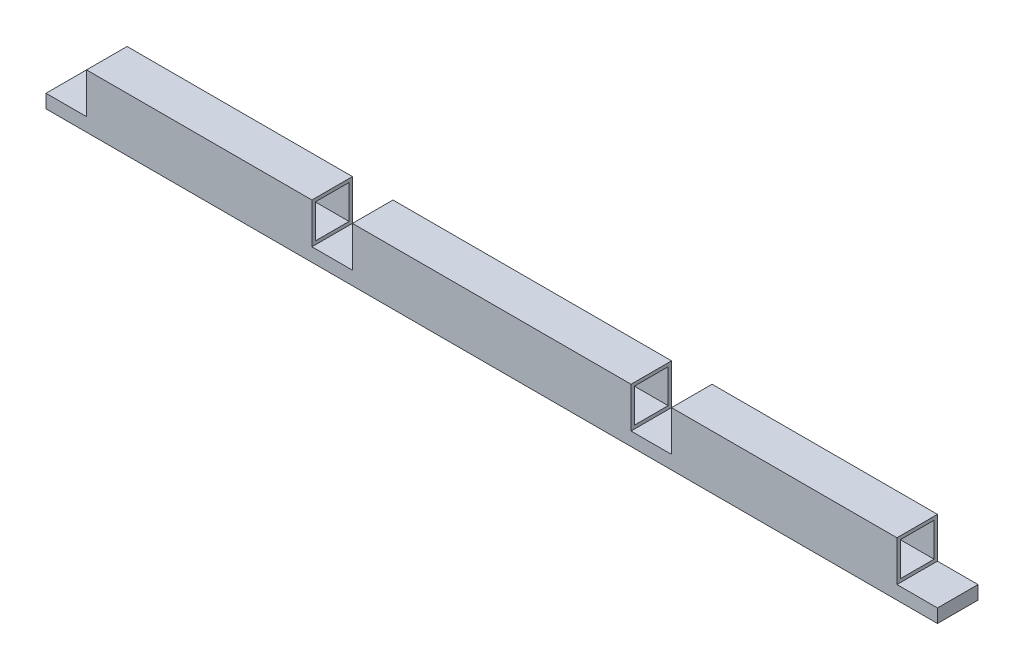
SolidWorks part; units mm, degrees
material "AISI 1020"
ref_plane "Front Plane" through (0, 0, 0) normal (0, 0, 1) x (1, 0, 0)
ref_plane "Top Plane" through (0, 0, 0) normal (0, 1, 0) x (1, 0, 0)
ref_plane "Right Plane" through (0, 0, 0) normal (1, 0, 0) x (0, 0, -1)
sketch "Sketch1" plane through (0, 0, 0) normal (0, 0, 1) x (1, 0, 0)
  line L1 (0, 0) -> (838.1, 0)
  line L2 (0, 0) -> (0, 12.7)
  line L3 (0, 12.7) -> (838.1, 12.7)
  line L4 (838.1, 0) -> (838.1, 12.7)
  dimension "D1" = 12.7
  dimension "D2" = 838.1
extrude "Boss-Extrude1" add sketch "Sketch1" against normal blind 38.1
sketch "Sketch2" plane through (0, 12.7, 0) normal (0, 1, 0) x (1, 0, 0)
  line L0 (838.1, 38.1) -> (0, 38.1) construction
  line L1 (0, 0) -> (38.1, 0) construction
  line L2 (0, 0) -> (0, 38.1) construction
  line L3 (0, 38.1) -> (38.1, 38.1) construction
  line L4 (38.1, 0) -> (38.1, 38.1) construction
  line L5 (838.1, 0) -> (0, 0) construction
  line L6 (250, 0) -> (288.1, 0) construction
  line L7 (250, 0) -> (250, 38.1) construction
  line L8 (250, 38.1) -> (288.1, 38.1) construction
  line L9 (288.1, 0) -> (288.1, 38.1) construction
  line L11 (550, 0) -> (588.1, 0) construction
  line L12 (550, 0) -> (550, 38.1) construction
  line L13 (550, 38.1) -> (588.1, 38.1) construction
  line L14 (588.1, 0) -> (588.1, 38.1) construction
  line L15 (838.1, 38.1) -> (800, 38.1) construction
  line L16 (838.1, 38.1) -> (838.1, 0) construction
  line L17 (838.1, 0) -> (800, 0) construction
  line L18 (800, 38.1) -> (800, 0) construction
  line L19 (38.1, 0) -> (250, 0)
  line L20 (38.1, 0) -> (38.1, 38.1)
  line L21 (38.1, 38.1) -> (250, 38.1)
  line L22 (250, 0) -> (250, 38.1)
  line L23 (288.1, 38.1) -> (550, 38.1)
  line L24 (288.1, 38.1) -> (288.1, 0)
  line L25 (288.1, 0) -> (550, 0)
  line L26 (550, 38.1) -> (550, 0)
  line L27 (800, 38.1) -> (588.1, 38.1)
  line L28 (800, 38.1) -> (800, 0)
  line L29 (800, 0) -> (588.1, 0)
  line L30 (588.1, 38.1) -> (588.1, 0)
  point P22 (19.05, 0)
  point P23 (269.05, 0)
  point P24 (569.05, 0)
  point P25 (819.05, 0)
  dimension "D1" = 38.1
  dimension "D2" = 38.1
  dimension "D3" = 38.1
  dimension "D4" = 250
  dimension "D5" = 250
  dimension "D6" = 38.1
  dimension "D7" = 300
extrude "Boss-Extrude2" add sketch "Sketch2" along normal blind 38.1
sketch "Sketch6" plane through (38.1, 0, 0) normal (-1, 0, 0) x (0, 0, 1)
  line L1 (0, 50.8) -> (-38.1, 50.8)
  line L2 (0, 50.8) -> (0, 12.7)
  line L3 (0, 12.7) -> (-38.1, 12.7)
  line L4 (-38.1, 50.8) -> (-38.1, 12.7)
  line L5 (-3.175, 15.875) -> (-34.925, 15.875)
  line L6 (-3.175, 15.875) -> (-3.175, 47.625)
  line L7 (-3.175, 47.625) -> (-34.925, 47.625)
  line L8 (-34.925, 15.875) -> (-34.925, 47.625)
  line L9 (-3.175, 15.875) -> (-34.925, 47.625) construction
  line L10 (-3.175, 47.625) -> (-34.925, 15.875) construction
  point P6 (-38.1, 31.75)
  point P7 (-19.05, 50.8)
  point P8 (-19.05, 31.75)
  point P11 (-19.05, 31.75)
  dimension "D1" = 3.175
extrude "Cut-Extrude2" cut sketch "Sketch6" against normal through all contours L6 L5 L8 L7
